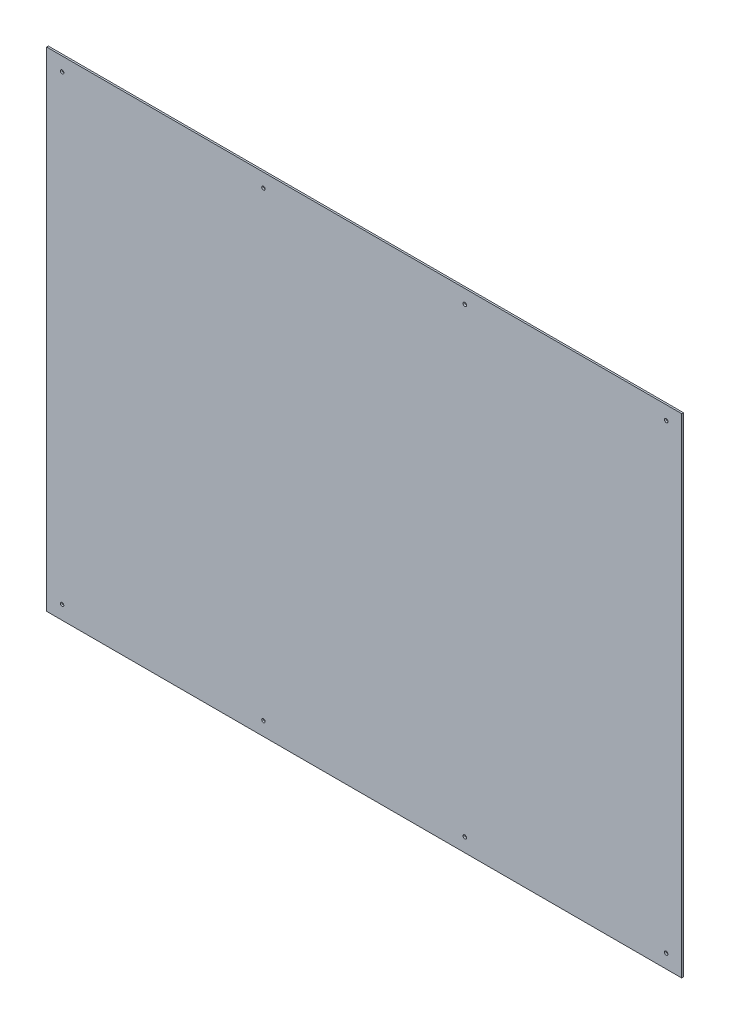
SolidWorks part; units mm, degrees
material "PC High Viscosity"
ref_plane "Front Plane" through (0, 0, 0) normal (0, 0, 1) x (1, 0, 0)
ref_plane "Top Plane" through (0, 0, 0) normal (0, 1, 0) x (1, 0, 0)
ref_plane "Right Plane" through (0, 0, 0) normal (1, 0, 0) x (0, 0, -1)
sketch "Sketch1" plane through (0, 0, 0) normal (0, 0, 1) x (1, 0, 0)
  line L1 (585.7875, -450.85) -> (-585.7875, -450.85)
  line L2 (585.7875, -450.85) -> (585.7875, 450.85)
  line L3 (585.7875, 450.85) -> (-585.7875, 450.85)
  line L4 (-585.7875, -450.85) -> (-585.7875, 450.85)
  line L5 (585.7875, -450.85) -> (-585.7875, 450.85) construction
  line L6 (585.7875, 450.85) -> (-585.7875, -450.85) construction
  point P0 (0, 0)
  dimension "D1" = 901.7
  dimension "D2" = 1171.575
extrude "Boss-Extrude1" add sketch "Sketch1" along normal blind 3.175
hole_wizard "1/4 (0.25) Diameter Hole1" positions "Sketch2" profile "Sketch3" hole size "1/4" standard "ANSI Inch" end condition through all
sketch "Sketch2" plane through (0, 0, 3.175) normal (0, 0, 1) x (1, 0, 0)
  line L0 (-585.7875, 450.85) -> (-585.7875, -450.85) construction
  line L1 (585.7875, 450.85) -> (-585.7875, 450.85) construction
  point P0 (-557.2125, 425.45)
  dimension "D1" = 28.575
  dimension "D2" = 25.4
sketch "Sketch3" plane through (-557.2125, 425.45, 3.175) normal (1, 0, 0) x (0, -1, 0)
  line L0 (0, 0) -> (0, 3.175)
  line L1 (0, 3.175) -> (3.175, 3.175)
  line L2 (3.175, 3.175) -> (3.175, 0)
  line L5 (3.175, 0) -> (0, 0)
  line L11 (0, -6.35) -> (0, 107.95) construction
  dimension "Thru Hole Dia." = 6.35
  dimension "Thru Hole Depth" = 3.175
pattern_linear "LPattern1" count 4 spacing 371.475 along (1, 0, 0) count 2 spacing 850.9 along (0, -1, 0) of "1/4 (0.25) Diameter Hole1"
